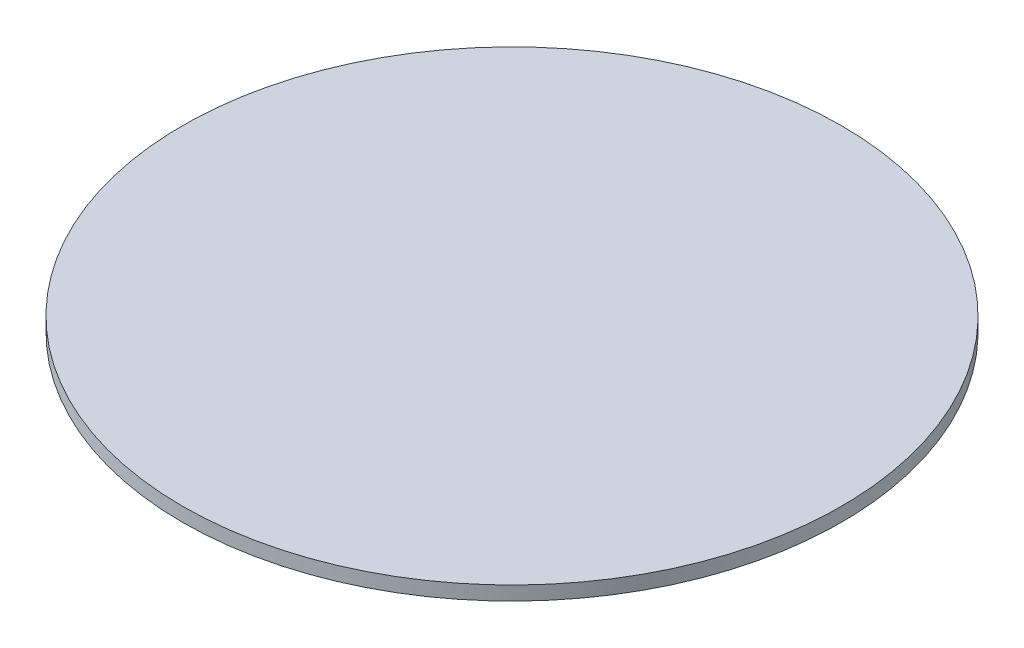
SolidWorks part; units mm, degrees
ref_plane "Front Plane" through (0, 0, 0) normal (0, 0, 1) x (1, 0, 0)
ref_plane "Top Plane" through (0, 0, 0) normal (0, 1, 0) x (1, 0, 0)
ref_plane "Right Plane" through (0, 0, 0) normal (1, 0, 0) x (0, 0, -1)
sketch "Sketch1" plane through (0, 0, 0) normal (0, 1, 0) x (1, 0, 0)
  circle A0 centre (0, 0) radius 150
  dimension "D1" = 300
extrude "Boss-Extrude1" add sketch "Sketch1" along normal blind 6.35
